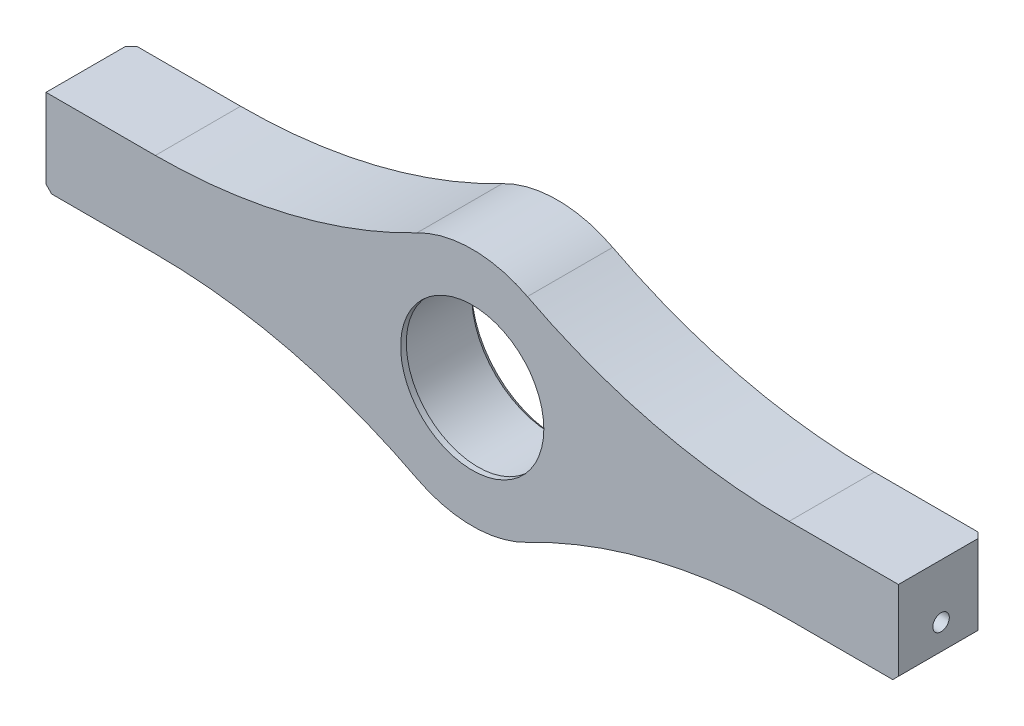
SolidWorks part; units mm, degrees
ref_plane "Ebene vorne" through (0, 0, 0) normal (0, 0, 1) x (1, 0, 0)
ref_plane "Ebene oben" through (0, 0, 0) normal (0, 1, 0) x (1, 0, 0)
ref_plane "Ebene rechts" through (0, 0, 0) normal (1, 0, 0) x (0, 0, -1)
sketch "Skizze1" plane through (0, 0, 0) normal (0, 0, 1) x (1, 0, 0)
  line L0 (19.7221, 7.5) -> (75, 7.5)
  line L1 (-75, -7.5) -> (-19.7221, -7.5)
  line L2 (-75, -7.5) -> (-75, 7.5)
  line L3 (-75, 7.5) -> (-19.7221, 7.5)
  line L4 (75, -7.5) -> (75, 7.5)
  line L5 (-75, -7.5) -> (75, 7.5) construction
  line L6 (-75, 7.5) -> (75, -7.5) construction
  line L7 (19.7221, -7.5) -> (75, -7.5)
  circle A0 centre (0, 0) radius 14.1
  arc A1 (19.7221, 7.5) -> (-19.7221, 7.5) centre (0, 0) ccw
  arc A2 (-19.7221, -7.5) -> (19.7221, -7.5) centre (0, 0) ccw
  point P0 (0, 0)
  dimension "D3" = 28.2
  dimension "D4" = 7
  dimension "D1" = 15
  dimension "D2" = 150
extrude "Aufsatz-Linear austragen1" add sketch "Skizze1" along normal blind 15
fillet "Verrundung1" radius 100 4 edges at (19.7221, -7.5, 7.5) (-19.7221, -7.5, 7.5) (-19.7221, 7.5, 7.5) (19.7221, 7.5, 7.5)
sketch "Skizze2" plane through (0, 0, 0) normal (0, 0, -1) x (-1, 0, 0)
  line L0 (-75, -7.5) -> (-75, 7.5) construction
  line L2 (0, 0) -> (0, 27.006) construction
  line L3 (-75, 7.5) -> (-55.758, 7.5) construction
  circle A0 centre (-67.5, 2) radius 1.4
  circle A1 centre (67.5, 2) radius 1.4
  dimension "D2" = 2.8
  dimension "D1" = 7.5
  dimension "D3" = 5.5
extrude "Schnitt-Linear austragen1" cut sketch "Skizze2" against normal blind 10
sketch "Skizze3" plane through (75, 0, 0) normal (1, 0, 0) x (0, 0, -1)
  line L0 (-7.5, -7.5) -> (-7.5, 7.5) construction
  line L2 (-15, -7.5) -> (0, -7.5) construction
  line L3 (-15, 7.5) -> (0, 7.5) construction
  circle A0 centre (-7.5, -2) radius 1.45
  dimension "D1" = 2.9
  dimension "D2" = 5.5
extrude "Schnitt-Linear austragen2" cut sketch "Skizze3" against normal blind 10
mirror "Spiegeln1" about plane through (0, 0, 0) normal (1, 0, 0) of "Schnitt-Linear austragen2"
sketch "Skizze5" plane through (0, 0, 0) normal (0, 0, 1) x (1, 0, 0)
  circle A0 centre (0, 0) radius 12.1
  circle A1 centre (0, 0) radius 14.1
  circle A2 centre (0, 0) radius 14.1 construction
  dimension "D1" = 2
extrude "Aufsatz-Linear austragen2" [suppressed] add sketch "Skizze5" along normal blind 6
sketch "Skizze6" plane through (0, 0, 15) normal (0, 0, 1) x (1, 0, 0)
  circle A0 centre (0, 0) radius 12.6
  circle A1 centre (0, 0) radius 14.1
  circle A4 centre (0, 0) radius 14.1 construction
  dimension "D1" = 1.5
extrude "Aufsatz-Linear austragen3" add sketch "Skizze6" against normal blind 1
chamfer "Fase1" distance 1 angle 45 1 edges at (14.1, 0, 0)
chamfer "Fase2" distance 1 angle 45 4 edges at (-75, -7.5, 7.5) (-75, 0, 0) (75, -7.5, 7.5) (75, 0, 0)
sketch "Skizze7" plane through (0, 0, 0) normal (0, 0, -1) x (-1, 0, 0)
  line L0 (27.295, 24.3463) -> (27.295, -22.8341)
  line L1 (27.295, -22.8341) -> (99.2753, -22.0024)
  line L2 (99.2753, -22.0024) -> (90.8827, 28.5048)
  line L3 (90.8827, 28.5048) -> (27.295, 24.3463)
  line L4 (0, 0) -> (0, 37.5779) construction
  line L5 (-90.8827, 28.5048) -> (-27.295, 24.3463)
  line L6 (-99.2753, -22.0024) -> (-90.8827, 28.5048)
  line L7 (-27.295, -22.8341) -> (-99.2753, -22.0024)
  line L8 (-27.295, 24.3463) -> (-27.295, -22.8341)
extrude "Schnitt-Linear austragen3" [suppressed] cut sketch "Skizze7" against normal through all
